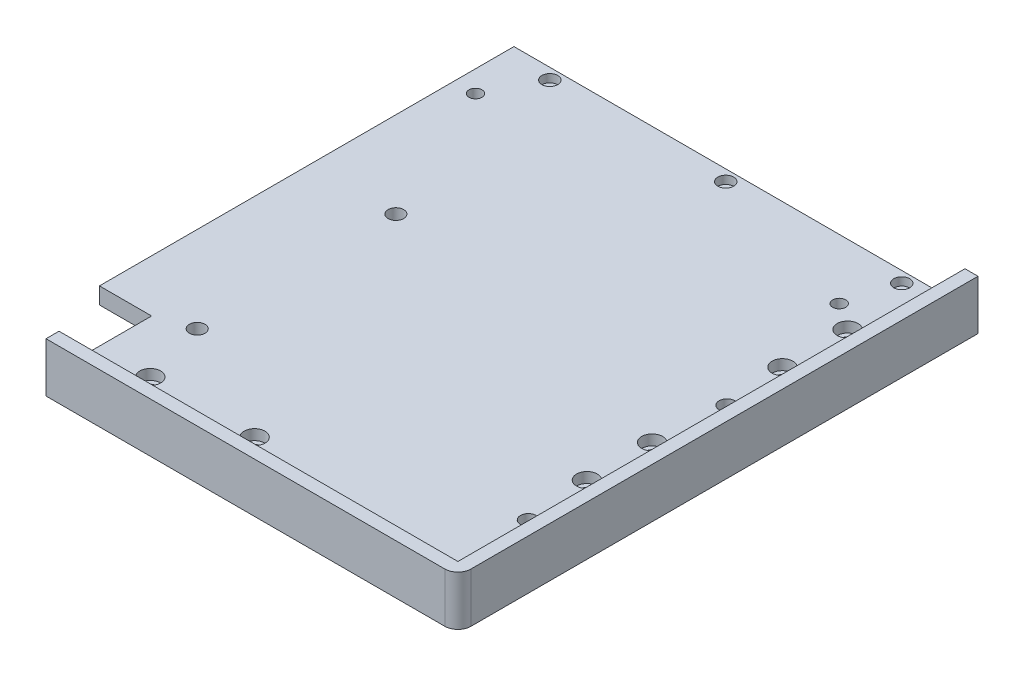
SolidWorks part; units mm, degrees
ref_plane "Front Plane" through (0, 0, 0) normal (0, 0, 1) x (1, 0, 0)
ref_plane "Top Plane" through (0, 0, 0) normal (0, 1, 0) x (1, 0, 0)
ref_plane "Right Plane" through (0, 0, 0) normal (1, 0, 0) x (0, 0, -1)
sketch "Sketch1" plane through (0, 0, 0) normal (0, 1, 0) x (1, 0, 0)
  line L1 (0, 0) -> (158, 0)
  line L2 (0, 0) -> (0, -199.5)
  line L3 (0, -199.5) -> (158, -199.5)
  line L4 (158, 0) -> (158, -199.5)
  dimension "D1" = 158
  dimension "D2" = 199.5
extrude "Boss-Extrude1" add sketch "Sketch1" along normal blind 6.35
sketch "Sketch2" [suppressed] plane through (0, 6.35, 0) normal (0, 1, 0) x (1, 0, 0)
  line L0 (0, -199.5) -> (158, -199.5) construction
  line L1 (158, -199.5) -> (77, -199.5)
  line L2 (158, -199.5) -> (158, -158.5)
  line L3 (158, -158.5) -> (77, -158.5)
  line L4 (77, -199.5) -> (77, -158.5)
  dimension "D1" = 81
  dimension "D2" = 41
sketch "Sketch3" plane through (0, 6.35, 0) normal (0, 1, 0) x (1, 0, 0)
  line L16 (158, -199.5) -> (158, 0) construction
  line L20 (0, -199.5) -> (158, -199.5) construction
  line L21 (158, -199.5) -> (158, 0)
  line L22 (0, -199.5) -> (158, -199.5)
  line L23 (0, -194.5) -> (153, -194.5)
  line L24 (153, -194.5) -> (153, 0)
  line L25 (158, 0) -> (153, 0)
  line L26 (0, -199.5) -> (0, -194.5)
  dimension "D1" = 5
extrude "Boss-Extrude2" add sketch "Sketch3" along normal blind 12.7
sketch "Sketch4" plane through (0, 6.35, 0) normal (0, -1, 0) x (1, 0, 0)
  line L0 (0, 179.5) -> (80, 179.5) construction
  line L1 (0, 0) -> (0, 199.5) construction
  line L3 (0, 199.5) -> (158, 199.5) construction
  line L4 (40, 179.5) -> (40, 188.5903) construction
  line L5 (138, 160) -> (138, 0) construction
  line L7 (158, 0) -> (0, 0) construction
  line L8 (158, 199.5) -> (158, 0) construction
  line L9 (138, 80) -> (152.6176, 80) construction
  point P8 (20, 179.5)
  point P11 (60, 179.5)
  point P20 (138, 130)
  point P21 (138, 105)
  point P22 (138, 30)
  point P23 (138, 80)
  point P24 (138, 55)
  dimension "D1" = 20
  dimension "D2" = 40
  dimension "D3" = 20
  dimension "D4" = 25
  dimension "D5" = 25
  dimension "D6" = 80
  dimension "D7" = 160
hole_wizard "CBORE for M4 SHCS1" positions "Sketch4" profile "Sketch5" counterbore size "M4" standard "ANSI Metric" end condition up to next
sketch "Sketch5" plane through (138, 6.35, 55) normal (1, 0, 0) x (0, 0, 1)
  line L0 (0, 0) -> (0, 6.35)
  line L1 (0, 6.35) -> (2.25, 6.35)
  line L3 (2.25, 6.35) -> (2.25, 4)
  line L4 (2.25, 4) -> (4, 4)
  line L5 (4, 4) -> (4, 0)
  line L7 (4, 0) -> (0, 0)
  line L11 (0, -6.35) -> (0, 107.95) construction
  dimension "Thru Hole Dia." = 4.5
  dimension "Thru Hole Depth" = 6.35
  dimension "C'Bore Dia." = 8
  dimension "C'Bore Depth" = 4
sketch "Sketch7" [suppressed] plane through (0, 0, 0) normal (0, 0, -1) x (-1, 0, 0)
  line L0 (-79, 19.05) -> (-79, 4.7647) construction
  line L1 (-158, 19.05) -> (0, 19.05) construction
  line L2 (-158, 19.05) -> (-158, 0) construction
  line L3 (-129, 19.05) -> (0, 19.05)
  line L4 (-129, 19.05) -> (-129, 9.05)
  line L5 (-129, 9.05) -> (0, 9.05)
  line L6 (0, 19.05) -> (0, 9.05)
  line L7 (0, 19.05) -> (0, 0) construction
  dimension "D2" = 10
  dimension "D3" = 29
extrude "Cut-Extrude2" [suppressed] cut sketch "Sketch7" against normal up to next
fillet "Fillet1" [suppressed] radius 5
fillet "Fillet2" [suppressed] radius 5
fillet "Fillet3" [suppressed] radius 5
sketch "Sketch8" [suppressed] plane through (0, 6.35, 0) normal (0, 1, 0) x (1, 0, 0)
  line L2 (153, 0) -> (153, -194.5) construction
  line L3 (153, 0) -> (0, 0) construction
  circle A0 centre (129.05, -62) radius 2.5
  circle A1 centre (129.05, -7.75) radius 2.5
  dimension "D1" = 5
  dimension "D2" = 54.25
  dimension "D3" = 23.95
  dimension "D4" = 7.75
extrude "eStop" [suppressed] cut sketch "Sketch8" against normal through all
sketch "Sketch9" [suppressed] plane through (0, 6.35, 0) normal (0, 1, 0) x (1, 0, 0)
  line L0 (153, 0) -> (0, 0) construction
  line L1 (81.1, -98.77) -> (16, -98.77) construction
  line L2 (81.1, -98.77) -> (81.1, -15.57) construction
  line L3 (81.1, -15.57) -> (16, -15.57) construction
  line L4 (16, -98.77) -> (16, -15.57) construction
  line L5 (81.1, -98.77) -> (16, -15.57) construction
  line L6 (81.1, -15.57) -> (16, -98.77) construction
  line L13 (0, 0) -> (0, -194.5) construction
  circle A0 centre (16, -15.57) radius 2.5
  circle A1 centre (81.1, -15.57) radius 2.5
  circle A2 centre (81.1, -98.77) radius 2.5
  circle A3 centre (16, -98.77) radius 2.5
  point P0 (48.55, -57.17)
  point P23 (138, -30)
  dimension "D5" = 5
  dimension "D7" = 16
  dimension "D1" = 83.2
  dimension "D2" = 65.1
  dimension "D6" = 57.17
extrude "NucleoAndPi" [suppressed] cut sketch "Sketch9" against normal through all
sketch "Sketch10" [suppressed] plane through (0, 6.35, 0) normal (0, 1, 0) x (1, 0, 0)
  line L1 (138, -72) -> (107.2, -72) construction
  line L2 (138, -72) -> (138, -89) construction
  line L3 (138, -89) -> (107.2, -89) construction
  line L4 (107.2, -72) -> (107.2, -89) construction
  line L5 (138, -72) -> (107.2, -89) construction
  line L6 (138, -89) -> (107.2, -72) construction
  circle A0 centre (138, -89) radius 1.2
  circle A1 centre (107.2, -72) radius 1.2
  circle A2 centre (138, -89) radius 2.7
  circle A3 centre (107.2, -72) radius 2.7
  circle A4 centre (129.05, -62) radius 2.5 construction
  point P0 (122.6, -80.5)
  point P18 (138, -55)
  dimension "D3" = 2.4
  dimension "D4" = 1.5
  dimension "D1" = 17
  dimension "D2" = 30.8
  dimension "D5" = 10
extrude "Bucks - Extrude" [suppressed] add sketch "Sketch10" along normal blind 3
sketch "Sketch11" [suppressed] plane through (0, 6.35, 0) normal (0, 1, 0) x (1, 0, 0)
  circle A0 centre (138, -89) radius 1.6
  circle A1 centre (107.2, -72) radius 1.6
  dimension "D1" = 3.2
extrude "Bucks - Cut" [suppressed] cut sketch "Sketch11" against normal up to next
pattern_linear "Buck 2" [suppressed] count 2 spacing 28
sketch "Sketch12" [suppressed] plane through (0, 6.35, 0) normal (0, 1, 0) x (1, 0, 0)
  line L1 (88, -179.5) -> (30, -179.5) construction
  line L2 (88, -179.5) -> (88, -130.5) construction
  line L3 (88, -130.5) -> (30, -130.5) construction
  line L4 (30, -179.5) -> (30, -130.5) construction
  circle A0 centre (30, -130.5) radius 2.5
  circle A1 centre (88, -130.5) radius 2.5
  circle A2 centre (88, -179.5) radius 2.5
  circle A3 centre (30, -179.5) radius 2.5
  point P4 (60, -179.5)
  point P12 (138, -130)
  dimension "D4" = 5
  dimension "D1" = 58
  dimension "D2" = 49
  dimension "D3" = 50
extrude "Pi" [suppressed] cut sketch "Sketch12" against normal through all
sketch "Sketch13" [suppressed] plane through (0, 6.35, 0) normal (0, 1, 0) x (1, 0, 0)
  line L1 (138, -159.18) -> (120.22, -159.18) construction
  line L2 (138, -159.18) -> (138, -179.5) construction
  line L3 (138, -179.5) -> (120.22, -179.5) construction
  line L4 (120.22, -159.18) -> (120.22, -179.5) construction
  circle A0 centre (120.22, -159.18) radius 1.6
  circle A1 centre (120.22, -179.5) radius 1.6
  circle A2 centre (138, -159.18) radius 1.6
  circle A3 centre (138, -179.5) radius 1.6
  point P8 (138, -130)
  point P9 (88, -179.5)
  dimension "D3" = 3.2
  dimension "D1" = 17.78
  dimension "D2" = 20.32
extrude "IMU" [suppressed] cut sketch "Sketch13" against normal through all
sketch "Sketch15" [suppressed] plane through (0, 6.35, 0) normal (0, 1, 0) x (1, 0, 0)
  line L0 (16, -15.57) -> (16, -98.77) construction
  line L1 (0, 0) -> (0, -194.5) construction
  line L3 (30, -130.5) -> (88, -130.5) construction
  line L4 (59, -115.385) -> (93.65, -115.385) construction
  line L5 (93.65, -98.77) -> (93.65, -115.385) construction
  line L6 (107.2, -72) -> (93.65, -72) construction
  line L7 (93.65, -98.77) -> (93.65, -72) construction
  line L8 (30, -130.5) -> (30, -179.5) construction
  circle A1 centre (5.5, -57.17) radius 3.05
  circle A2 centre (5.5, -98.77) radius 3.05
  circle A3 centre (16, -115.385) radius 3.05
  circle A4 centre (59, -115.385) radius 3.05
  circle A5 centre (93.65, -98.77) radius 3.05
  circle A6 centre (93.65, -115.385) radius 3.05
  circle A7 centre (93.65, -72) radius 3.05
  circle A8 centre (16, -155) radius 3.05
  point P1 (16, -57.17)
  point P21 (59, -130.5)
  point P24 (81.1, -98.77)
  point P36 (30, -155)
  dimension "D1" = 6.1
  dimension "D2" = 16.615
  dimension "D3" = 12.55
  dimension "D4" = 5.5
extrude "MAGNETS" [suppressed] cut sketch "Sketch15" against normal blind 3.1
ref_plane "Plane1" through (0, 0, 99.75) normal (0, 0, -1) x (-1, 0, 0)
sketch "Sketch16" plane through (0, 0, 194.5) normal (0, 0, -1) x (-1, 0, 0)
  line L4 (-153, 6.35) -> (0, 6.35)
  line L5 (0, 6.35) -> (0, 19.05)
  line L6 (0, 19.05) -> (-153, 19.05)
  line L7 (-153, 19.05) -> (-153, 6.35)
  line L8 (-153, 6.35) -> (0, 6.35)
  line L9 (0, 6.35) -> (0, 19.05)
  line L10 (0, 19.05) -> (-153, 19.05)
  line L11 (-153, 19.05) -> (-153, 6.35)
  dimension "D1" = 0
fillet "Fillet4" radius 5 1 edges at (158, 9.525, 199.5)
sketch "Sketch17" plane through (0, 6.35, 0) normal (0, 1, 0) x (1, 0, 0)
  line L0 (0, -199.5) -> (153, -199.5) construction
  line L1 (0, 0) -> (-20, 0)
  line L2 (0, 0) -> (0, -159)
  line L3 (0, -159) -> (-20, -159)
  line L4 (-20, 0) -> (-20, -159)
  dimension "D1" = 40.5
  dimension "D2" = 20
extrude "Boss-Extrude3" add sketch "Sketch17" against normal up to surface (6.35 mm away) up to face at (20, 0, 181.75)
sketch "Sketch18" plane through (0, 6.35, 0) normal (0, 1, 0) x (1, 0, 0)
  line L1 (13, -154.5) -> (140, -154.5) construction
  line L2 (13, -154.5) -> (13, -78.3) construction
  line L3 (13, -78.3) -> (140, -78.3) construction
  line L4 (140, -154.5) -> (140, -78.3) construction
  line L5 (13, -154.5) -> (140, -78.3) construction
  line L6 (13, -78.3) -> (140, -154.5) construction
  line L7 (153, -194.5) -> (0, -194.5) construction
  line L8 (153, 0) -> (153, -194.5) construction
  circle A0 centre (13, -154.5) radius 3
  circle A1 centre (13, -78.3) radius 3
  circle A2 centre (140, -78.3) radius 3
  circle A3 centre (140, -154.5) radius 3
  point P0 (76.5, -116.4)
  dimension "D5" = 6
  dimension "D1" = 76.2
  dimension "D2" = 127
  dimension "D3" = 40
  dimension "D4" = 13
extrude "Enclosure" cut sketch "Sketch18" against normal through all
sketch "Sketch19" plane through (0, 6.35, 0) normal (0, 1, 0) x (1, 0, 0)
  line L0 (-11.75, -23) -> (127.75, -23) construction
  line L1 (158, -194.5) -> (158, 0) construction
  line L2 (153, 0) -> (-20, 0) construction
  circle A0 centre (-11.75, -23) radius 2.5
  circle A1 centre (127.75, -23) radius 2.5
  point P6 (58, -23)
  dimension "D3" = 5
  dimension "D1" = 139.5
  dimension "D2" = 100
  dimension "D4" = 23
extrude "Cut-Extrude4" cut sketch "Sketch19" against normal through all
sketch "Sketch20" plane through (0, 6.35, 0) normal (0, 1, 0) x (1, 0, 0)
  line L0 (153, -4.25) -> (42.3051, -4.25) construction
  line L1 (153, 0) -> (153, -194.5) construction
  line L2 (153, 0) -> (-20, 0) construction
  line L3 (153, 0) -> (153, -194.5) construction
  circle A0 centre (133, -4.25) radius 3.05
  circle A1 centre (65.5, -4.25) radius 3.05
  circle A2 centre (-2, -4.25) radius 3.05
  dimension "D1" = 6.1
  dimension "D5" = 67.5
  dimension "D2" = 4.25
  dimension "D3" = 20
  dimension "D4" = 67.5
extrude "Cut-Extrude5" cut sketch "Sketch20" against normal blind 3.1
